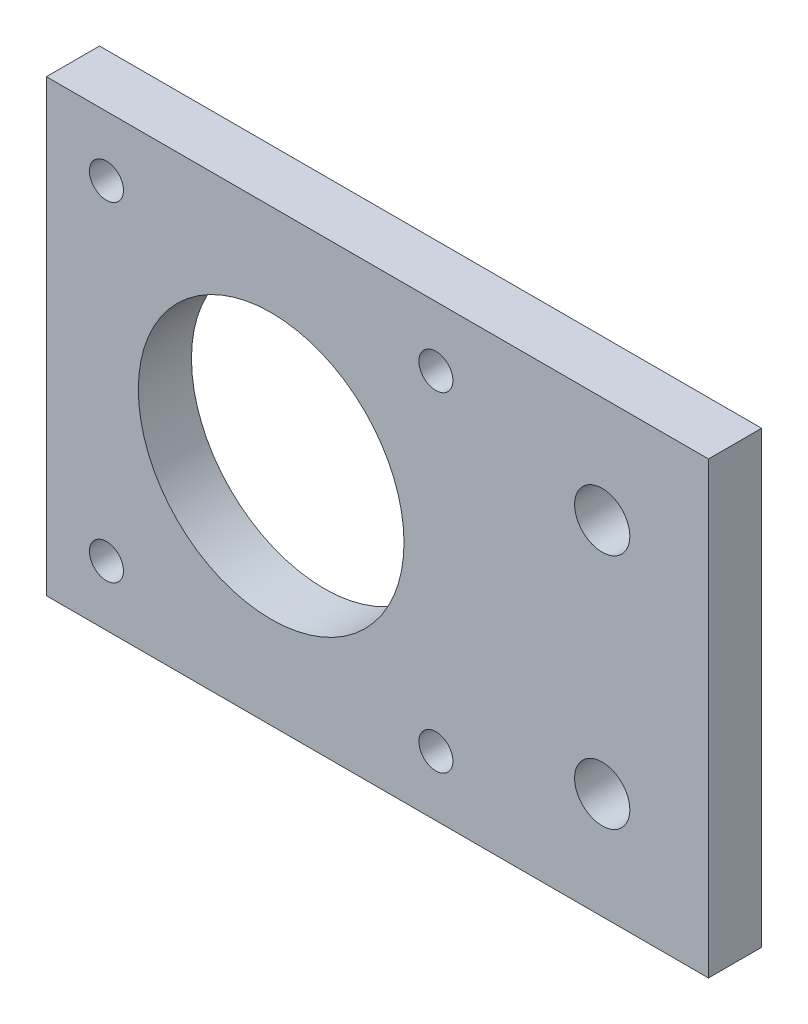
SolidWorks part; units mm, degrees
material "PET"
ref_plane "Front Plane" through (0, 0, 0) normal (0, 0, 1) x (1, 0, 0)
ref_plane "Top Plane" through (0, 0, 0) normal (0, 1, 0) x (1, 0, 0)
ref_plane "Right Plane" through (0, 0, 0) normal (1, 0, 0) x (0, 0, -1)
sketch "Sketch2" plane through (0, 0, 0) normal (0, 0, 1) x (1, 0, 0)
  line L0 (-21.15, 21.15) -> (21.15, -21.15) construction
  line L1 (-21.15, 21.15) -> (21.15, 21.15)
  line L2 (-21.15, 21.15) -> (-21.15, -21.15)
  line L3 (-21.15, -21.15) -> (21.15, -21.15)
  line L4 (21.15, 21.15) -> (21.15, -21.15)
  line L5 (21.15, 21.15) -> (41.15, 21.15)
  line L6 (21.15, 21.15) -> (21.15, -21.15)
  line L7 (21.15, -21.15) -> (41.15, -21.15)
  line L8 (41.15, 21.15) -> (41.15, -21.15)
  line L9 (31.15, 21.15) -> (31.15, -21.15) construction
  line L10 (-15.5, -15.5) -> (15.5, 15.5) construction
  circle A0 centre (31.15, 11.15) radius 2.6
  circle A1 centre (31.15, -11.15) radius 2.6
  circle A2 centre (-15.5, 15.5) radius 1.6
  circle A3 centre (15.5, -15.5) radius 1.6
  circle A4 centre (15.5, 15.5) radius 1.6
  circle A5 centre (-15.5, -15.5) radius 1.6
  dimension "D4" = 5.2
  dimension "D5" = 5.2
  dimension "D8" = 3.2
  dimension "D9" = 3.2
  dimension "D10" = 3.2
  dimension "D11" = 3.2
  dimension "D1" = 20
  dimension "D2" = 42.3
  dimension "D3" = 42.3
  dimension "D6" = 10
  dimension "D7" = 10
  dimension "D12" = 31
  dimension "D13" = 31
extrude "Boss-Extrude1" add sketch "Sketch2" along normal blind 5 contours L4 L1 L2 L3 A5 A4 A3 A2 | L8 L5 L4 L7 A1 A0
sketch "Sketch3" plane through (0, 0, 0) normal (0, 0, -1) x (-1, 0, 0)
  circle A0 centre (0, 0) radius 12.5
  dimension "D1" = 25
extrude "Cut-Extrude1" cut sketch "Sketch3" against normal blind 10
